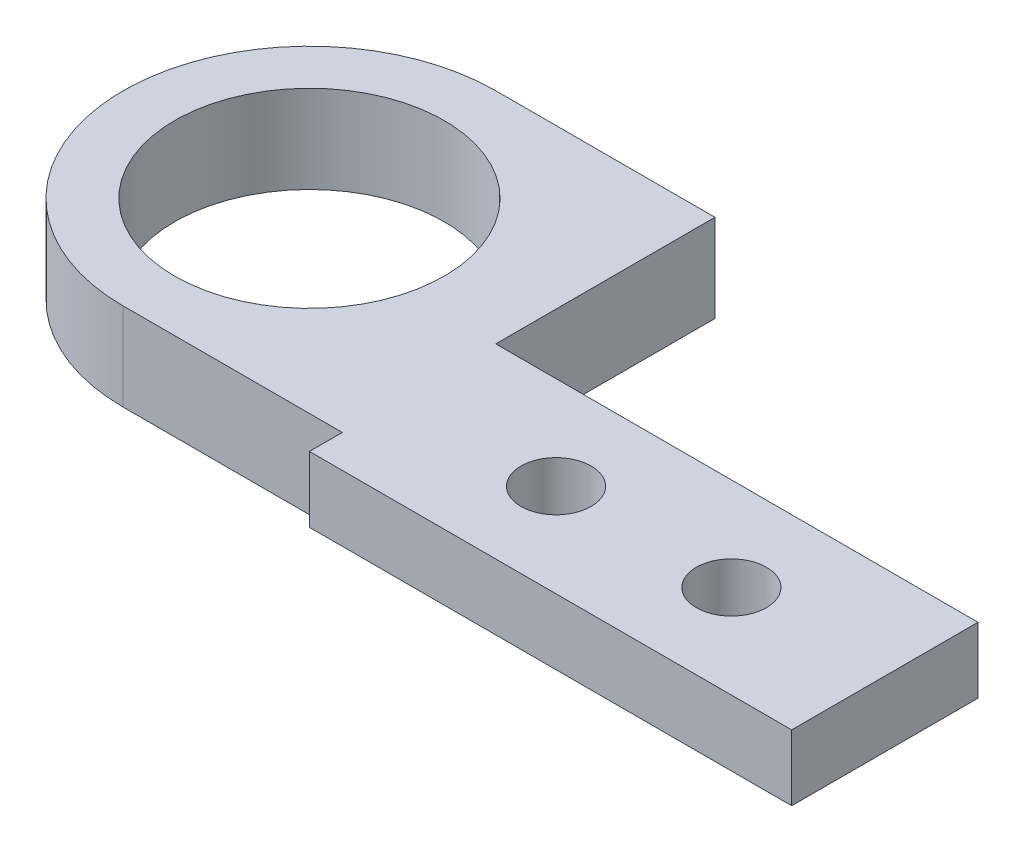
SolidWorks part; units mm, degrees
ref_plane "Front Plane" through (0, 0, 0) normal (0, 0, 1) x (1, 0, 0)
ref_plane "Top Plane" through (0, 0, 0) normal (0, 1, 0) x (1, 0, 0)
ref_plane "Right Plane" through (0, 0, 0) normal (1, 0, 0) x (0, 0, -1)
sketch "Sketch1" plane through (0, 0, 0) normal (0, 1, 0) x (1, 0, 0)
  line L0 (-16.2891, 0) -> (-7.7891, 0)
  line L1 (-7.7891, -8.5) -> (2.2109, -8.5)
  line L3 (-7.7891, 8.5) -> (2.2109, 8.5)
  line L4 (2.2109, -8.5) -> (2.2109, 8.5)
  line L5 (-1.4822, -5.6986) -> (2.2109, 8.5) construction
  line L6 (-2.8495, 10.955) -> (2.2109, -8.5) construction
  arc A0 (-7.7891, 8.5) -> (-1.4822, -5.6986) centre (-7.7891, 0) ccw
  arc A1 (-7.7891, 8.5) -> (-7.7891, -8.5) centre (-7.7891, 0) ccw
  circle A2 centre (-7.7891, 0) radius 6.15
  point P0 (0, 0)
  dimension "D1" = 12.3
  dimension "D2" = 10
  dimension "D3" = 8.5
  dimension "D4" = 17
extrude "Boss-Extrude1" add sketch "Sketch1" along normal blind 4
sketch "Sketch4" plane through (0, 4, 0) normal (0, 1, 0) x (1, 0, 0)
  line L0 (24.2109, -1.5) -> (2.2109, -1.5)
  line L2 (2.2109, -1.5) -> (2.2109, -8.5)
  line L4 (24.2109, -1.5) -> (24.2109, -8.5)
  line L5 (2.2109, -8.5) -> (2.2109, 8.5) construction
  line L7 (2.2109, -8.5) -> (2.2109, -10)
  line L8 (2.2109, -10) -> (24.2109, -10)
  line L9 (24.2109, -8.5) -> (24.2109, -10)
  dimension "D1" = 22
  dimension "D2" = 7
  dimension "D3" = 1.5
  dimension "D4" = 22
extrude "Boss-Extrude3" add sketch "Sketch4" against normal blind 3
sketch "Sketch5" plane through (0, 4, 0) normal (0, 1, 0) x (1, 0, 0)
  line L0 (2.2109, -10) -> (24.2109, -10) construction
  line L1 (2.2109, -8.5) -> (2.2109, -10) construction
  line L2 (24.2109, -10) -> (24.2109, -1.5) construction
  circle A0 centre (9.2109, -5.75) radius 1.6
  circle A1 centre (17.2109, -5.75) radius 1.6
  dimension "D2" = 3.2
  dimension "D5" = 3.2
  dimension "D1" = 4.25
  dimension "D3" = 7
  dimension "D4" = 4.25
  dimension "D6" = 7
extrude "Cut-Extrude1" cut sketch "Sketch5" against normal blind 10
